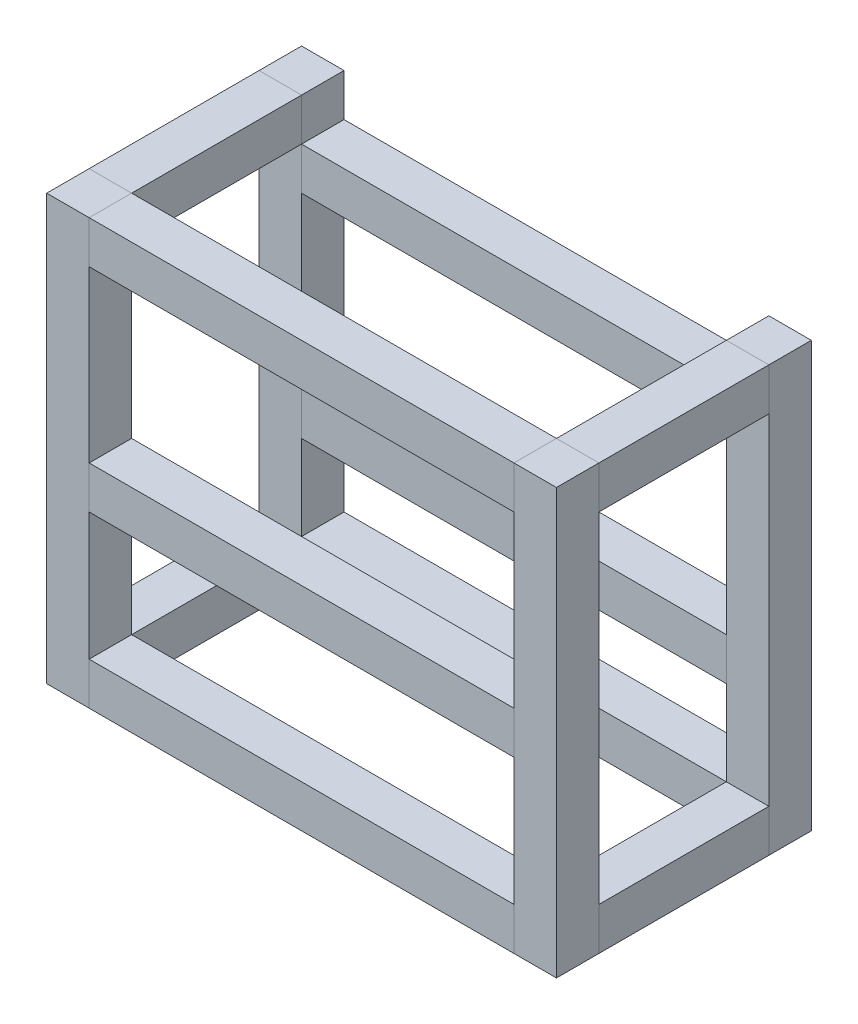
SolidWorks part; units mm, degrees
material "6061 Alloy"
ref_plane "Front Plane" through (0, 0, 0) normal (0, 0, 1) x (1, 0, 0)
ref_plane "Top Plane" through (0, 0, 0) normal (0, 1, 0) x (1, 0, 0)
ref_plane "Right Plane" through (0, 0, 0) normal (1, 0, 0) x (0, 0, -1)
sketch "Sketch1" plane through (0, 0, 0) normal (0, 1, 0) x (1, 0, 0)
  line L1 (-152.4, -76.2) -> (152.4, -76.2)
  line L2 (-152.4, -76.2) -> (-152.4, 76.2)
  line L3 (-152.4, 76.2) -> (152.4, 76.2)
  line L4 (152.4, -76.2) -> (152.4, 76.2)
  line L5 (-152.4, -76.2) -> (152.4, 76.2) construction
  line L6 (-152.4, 76.2) -> (152.4, -76.2) construction
  line L7 (-152.4, 76.2) -> (-127, 76.2)
  line L8 (-152.4, 76.2) -> (-152.4, 50.8)
  line L9 (-152.4, 50.8) -> (-127, 50.8)
  line L10 (-127, 76.2) -> (-127, 50.8)
  line L11 (152.4, 76.2) -> (127, 76.2)
  line L12 (152.4, 76.2) -> (152.4, 50.8)
  line L13 (152.4, 50.8) -> (127, 50.8)
  line L14 (127, 76.2) -> (127, 50.8)
  line L15 (-152.4, -76.2) -> (-127, -76.2)
  line L16 (-152.4, -76.2) -> (-152.4, -50.8)
  line L17 (-152.4, -50.8) -> (-127, -50.8)
  line L18 (-127, -76.2) -> (-127, -50.8)
  line L19 (152.4, -76.2) -> (127, -76.2)
  line L20 (152.4, -76.2) -> (152.4, -50.8)
  line L21 (152.4, -50.8) -> (127, -50.8)
  line L22 (127, -76.2) -> (127, -50.8)
  point P0 (0, 0)
  dimension "D1" = 25.4
  dimension "D2" = 254
  dimension "D3" = 101.6
extrude "Boss-Extrude1" add sketch "Sketch1" along normal blind 254 contours L10 L3 L2 L9 | L1 L18 L17 L2 | L22 L1 L4 L21 | L3 L14 L13 L4
sketch "Sketch2" plane through (0, 0, 0) normal (1, 0, 0) x (0, 0, -1)
  line L0 (-76.2, 254) -> (-76.2, 0) construction
  line L1 (-76.2, 254) -> (-50.8, 254)
  line L2 (-76.2, 254) -> (-76.2, 228.6)
  line L3 (-76.2, 228.6) -> (-50.8, 228.6)
  line L4 (-50.8, 254) -> (-50.8, 228.6)
  line L5 (50.8, 228.6) -> (76.2, 228.6)
  line L6 (50.8, 228.6) -> (50.8, 203.2)
  line L7 (50.8, 203.2) -> (76.2, 203.2)
  line L8 (76.2, 228.6) -> (76.2, 203.2)
  line L9 (-76.2, 25.4) -> (-50.8, 25.4)
  line L10 (-76.2, 25.4) -> (-76.2, 0)
  line L11 (-76.2, 0) -> (-50.8, 0)
  line L12 (-50.8, 25.4) -> (-50.8, 0)
  line L13 (50.8, 25.4) -> (76.2, 25.4)
  line L14 (50.8, 25.4) -> (50.8, 0)
  line L15 (50.8, 0) -> (76.2, 0)
  line L16 (76.2, 25.4) -> (76.2, 0)
  line L17 (-76.2, 127) -> (-50.8, 127)
  line L18 (-76.2, 127) -> (-76.2, 101.6)
  line L19 (-76.2, 101.6) -> (-50.8, 101.6)
  line L20 (-50.8, 127) -> (-50.8, 101.6)
  line L21 (50.8, 101.6) -> (76.2, 101.6)
  line L22 (50.8, 101.6) -> (50.8, 76.2)
  line L23 (50.8, 76.2) -> (76.2, 76.2)
  line L24 (76.2, 101.6) -> (76.2, 76.2)
  line L25 (76.2, 254) -> (76.2, 0) construction
  line L26 (-76.2, 0) -> (-50.8, 0) construction
  line L27 (76.2, 0) -> (50.8, 0) construction
  dimension "D1" = 25.4
  dimension "D2" = 254
  dimension "D3" = 127
  dimension "D4" = 101.6
  dimension "D5" = 228.6
extrude "Boss-Extrude2" add sketch "Sketch2" along normal up to next (127 mm away) and the other way up to next (127 mm away) separate body
sketch "Sketch3" plane through (0, 0, 0) normal (0, 0, 1) x (1, 0, 0)
  line L1 (-152.4, 254) -> (-127, 254)
  line L2 (-152.4, 254) -> (-152.4, 228.6)
  line L3 (-152.4, 228.6) -> (-127, 228.6)
  line L4 (-127, 254) -> (-127, 228.6)
  line L5 (-152.4, 25.4) -> (-127, 25.4)
  line L6 (-152.4, 25.4) -> (-152.4, 0)
  line L7 (-152.4, 0) -> (-127, 0)
  line L8 (-127, 25.4) -> (-127, 0)
  line L9 (127, 254) -> (152.4, 254)
  line L10 (127, 254) -> (127, 228.6)
  line L11 (127, 228.6) -> (152.4, 228.6)
  line L12 (152.4, 254) -> (152.4, 228.6)
  line L13 (127, 25.4) -> (152.4, 25.4)
  line L14 (127, 25.4) -> (127, 0)
  line L15 (127, 0) -> (152.4, 0)
  line L16 (152.4, 25.4) -> (152.4, 0)
  dimension "D1" = 25.4
extrude "Boss-Extrude3" add sketch "Sketch3" along normal up to next (50.8 mm away) and the other way up to next (50.8 mm away) separate body
